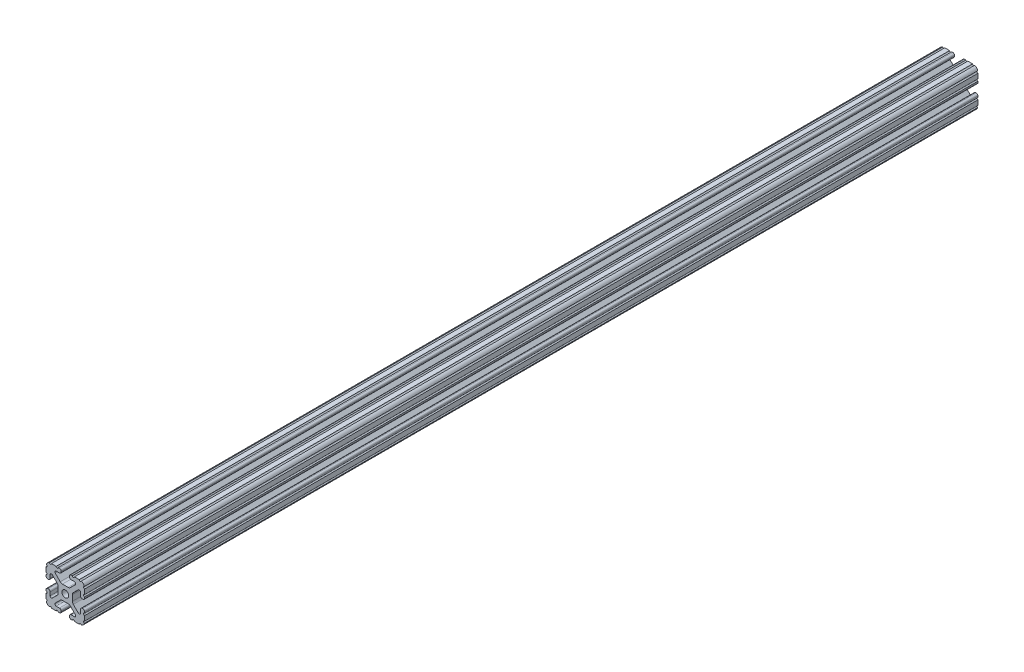
SolidWorks part; units mm, degrees
ref_plane "Front Plane" through (0, 0, 0) normal (0, 0, 1) x (1, 0, 0)
ref_plane "Top Plane" through (0, 0, 0) normal (0, 1, 0) x (1, 0, 0)
ref_plane "Right Plane" through (0, 0, 0) normal (1, 0, 0) x (0, 0, -1)
sketch "Sketch2" plane through (0, 0, 0) normal (0, 0, 1) x (1, 0, 0)
  line L0 (0, 19.05) -> (0, -19.05) construction
  line L1 (-19.05, 0) -> (19.05, 0) construction
  line L2 (4.064, -19.05) -> (19.05, -19.05)
  line L3 (19.05, -19.05) -> (19.05, -4.064)
  line L4 (4.064, -19.05) -> (4.064, -14.986)
  line L5 (4.064, -14.986) -> (12.1123, -14.986)
  line L6 (12.1123, -14.986) -> (4.1113, -6.985)
  line L7 (0, 0) -> (19.05, -19.05) construction
  line L8 (19.05, -4.064) -> (14.986, -4.064)
  line L9 (14.986, -4.064) -> (14.986, -12.1123)
  line L10 (14.986, -12.1123) -> (6.985, -4.1113)
  circle A0 centre (0, 0) radius 3.3274
  arc A1 (8.9963, -14.986) -> (9.909, -12.7826) centre (8.9963, -13.6953) ccw construction
  point P8 (0, -6.985)
  dimension "Center Hole Diameter" = 6.6548
  dimension "Rail Height" = 38.1
  dimension "Rail Width" = 38.1
  dimension "T-Slot Width" = 8.128
  dimension "Slot Inner Width" = 20.574
  dimension "Thickness" = 4.064
  dimension "Slot Depth" = 8.001
  dimension "D1" = 4.064
sketch "Sketch3" plane through (0, 0, 0) normal (1, 0, 0) x (0, 0, -1)
  line L0 (-457.2, -19.05) -> (457.2, -19.05) construction
  line L1 (-431.8, 0) -> (431.8, 0) construction
  dimension "Length" = 914.4
  dimension "D1" = 25.4
sketch "Sketch4" plane through (0, 0, 0) normal (0, 0, 1) x (1, 0, 0)
  line L0 (5.7912, -19.05) -> (14.3002, -19.05)
  line L1 (4.064, -19.05) -> (19.05, -19.05) construction
  line L2 (4.064, -19.05) -> (4.064, -14.986) construction
  line L3 (4.064, -14.986) -> (12.1123, -14.986) construction
  line L4 (4.064, -16.7132) -> (4.064, -17.3228)
  line L5 (5.7912, -14.986) -> (8.9963, -14.986)
  line L6 (0, -6.985) -> (2.833, -6.985)
  line L7 (12.1123, -14.986) -> (4.1113, -6.985) construction
  line L8 (5.0152, -7.8889) -> (9.909, -12.7826)
  line L9 (19.05, -19.05) -> (19.05, -4.064) construction
  line L10 (14.986, -12.1123) -> (6.985, -4.1113) construction
  line L11 (14.986, -4.064) -> (14.986, -12.1123) construction
  line L12 (14.986, -8.9963) -> (14.986, -5.7912)
  line L13 (19.05, -4.064) -> (14.986, -4.064) construction
  line L14 (16.7132, -4.064) -> (17.3228, -4.064)
  line L15 (19.05, -5.7912) -> (19.05, -14.3002)
  line L16 (12.7826, -9.909) -> (7.8889, -5.0152)
  line L17 (6.985, 0) -> (6.985, -2.833)
  line L18 (-19.05, 0) -> (19.05, 0) construction
  line L19 (0, -6.985) -> (0, -3.3274)
  line L20 (0, 19.05) -> (0, -19.05) construction
  line L21 (6.985, 0) -> (3.3274, 0)
  arc A0 (4.064, -17.3228) -> (5.7912, -19.05) centre (5.7912, -17.3228) ccw
  arc A2 (4.064, -16.7132) -> (5.7912, -14.986) centre (5.7912, -16.7132) cw
  arc A3 (8.9963, -14.986) -> (9.909, -12.7826) centre (8.9963, -13.6953) ccw
  arc A4 (2.833, -6.985) -> (5.0152, -7.8889) centre (2.833, -10.0711) cw
  arc A5 (14.3002, -19.05) -> (19.05, -14.3002) centre (14.3002, -14.3002) ccw
  arc A6 (12.7826, -9.909) -> (14.986, -8.9963) centre (13.6953, -8.9963) ccw
  arc A7 (14.986, -5.7912) -> (16.7132, -4.064) centre (16.7132, -5.7912) cw
  arc A8 (17.3228, -4.064) -> (19.05, -5.7912) centre (17.3228, -5.7912) cw
  arc A9 (7.8889, -5.0152) -> (6.985, -2.833) centre (10.0711, -2.833) cw
  circle A10 centre (0, 0) radius 3.3274 construction
  arc A11 (0, -3.3274) -> (3.3274, 0) centre (0, 0) ccw
  dimension "D1" = 4.7498
  dimension "D2" = 3.0861
  dimension "D3" = 1.7272
extrude "Boss-Extrude1" add sketch "Sketch4" along normal mid plane 881.634
sketch "Sketch5" plane through (0, 0, 0) normal (0, 0, 1) x (1, 0, 0)
  line L0 (4.064, -19.05) -> (19.05, -19.05) construction
  line L1 (5.7912, -14.986) -> (8.9963, -14.986) construction
  line L3 (0, 0) -> (19.05, -19.05) construction
  line L4 (8.9963, -14.986) -> (8.9963, -19.05) construction
  line L5 (12.1123, -14.986) -> (4.1113, -6.985) construction
  circle A0 centre (14.7395, -19.05) radius 1.016
  circle A1 centre (7.9803, -19.05) radius 1.016
  circle A2 centre (19.05, -14.7395) radius 1.016
  circle A3 centre (19.05, -7.9803) radius 1.016
  point P10 (7.3938, -14.986)
  point P12 (13.6953, -8.9963)
  dimension "D1" = 2.032
extrude "Cut-Extrude1" cut sketch "Sketch5" against normal through all both and the other way through all
mirror "Mirror1" about plane through (0, 0, 0) normal (1, 0, 0) of bodies 137 134
mirror "Mirror2" about plane through (0, 0, 0) normal (0, 1, 0) of bodies 135
equation "\"D1@Boss-Extrude1\"=\"Length@Sketch3\""
equation "\"D1@Sketch2\"=\"Thickness@Sketch2\""
equation "\"D2@Sketch4\"=\"Slot Inner Width@Sketch2\"*0.15"
equation "\"D1@Sketch4\"=\"D3@Sketch4\"*2.75"
equation "\"D3@Sketch4\"=\"Thickness@Sketch2\"*0.425"
equation "\"D1@Sketch5\"=\"Thickness@Sketch2\"*0.5"
